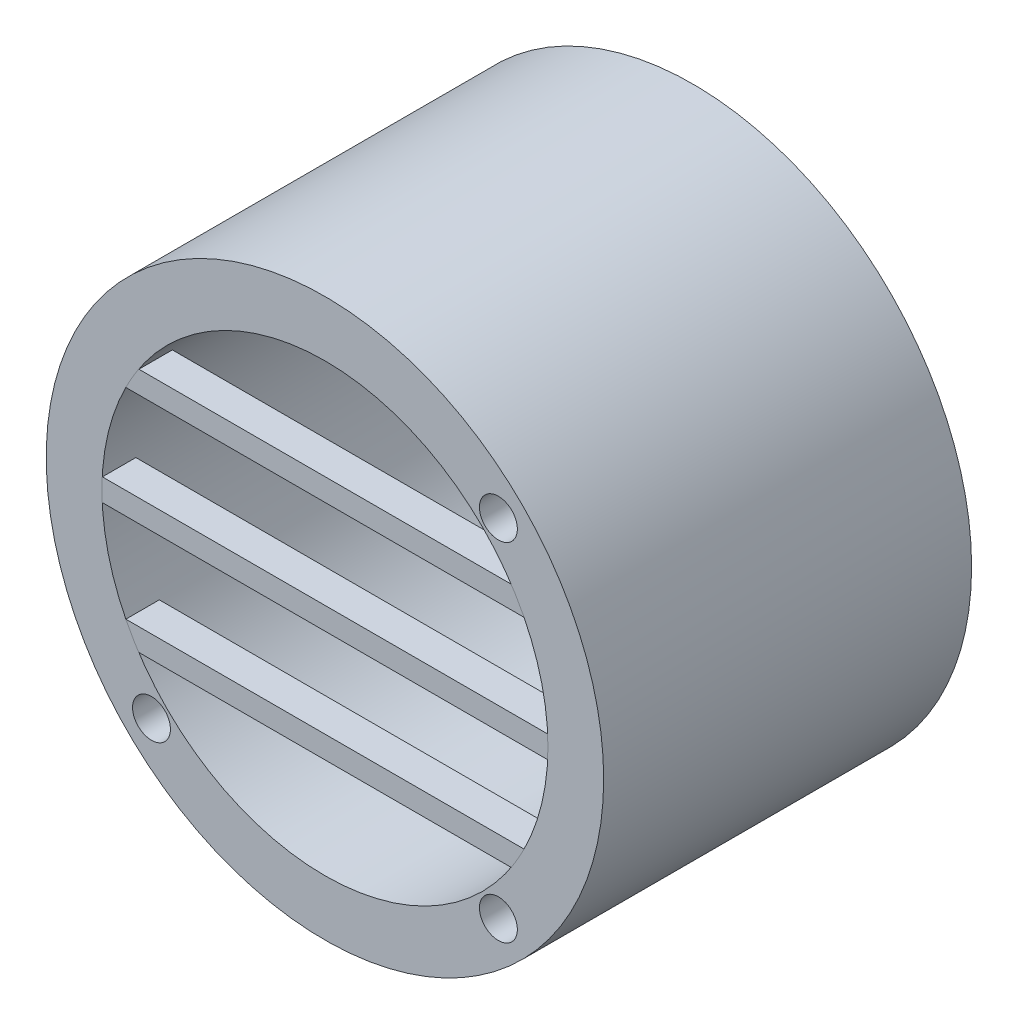
SolidWorks part; units mm, degrees
ref_plane "Front Plane" through (0, 0, 0) normal (0, 0, 1) x (1, 0, 0)
ref_plane "Top Plane" through (0, 0, 0) normal (0, 1, 0) x (1, 0, 0)
ref_plane "Right Plane" through (0, 0, 0) normal (1, 0, 0) x (0, 0, -1)
sketch "Sketch2" plane through (0, 0, 0) normal (0, 0, 1) x (1, 0, 0)
  circle A0 centre (0, 0) radius 25
  circle A1 centre (0, 0) radius 20
  dimension "D1" = 50
  dimension "D2" = 40
extrude "Boss-Extrude1" add sketch "Sketch2" along normal blind 33
sketch "Sketch3" plane through (0, 0, 33) normal (0, 0, 1) x (1, 0, 0)
  line L5 (-20, 0) -> (20, 0) construction
  line L6 (-20, -10) -> (20, -10)
  line L22 (-20, 10) -> (20, 10)
  line L24 (-20, -1) -> (20, -1)
  line L27 (-20, -1) -> (-20, 1)
  line L28 (-20, 1) -> (20, 1)
  line L29 (20, -1) -> (20, 1)
  line L30 (-20, -1) -> (20, 1) construction
  line L31 (-20, 1) -> (20, -1) construction
  line L32 (-20, 9) -> (20, 9)
  line L33 (-20, 9) -> (-20, 11)
  line L36 (-20, 11) -> (20, 11)
  line L37 (20, 9) -> (20, 11)
  line L38 (-20, 9) -> (20, 11) construction
  line L39 (-20, 11) -> (20, 9) construction
  line L42 (-20, -11) -> (20, -11)
  line L43 (-20, -11) -> (-20, -9)
  line L46 (-20, -9) -> (20, -9)
  line L47 (20, -11) -> (20, -9)
  line L50 (-20, -11) -> (20, -9) construction
  line L51 (-20, -9) -> (20, -11) construction
  circle A1 centre (0, 0) radius 20
  point P0 (0, 0)
  point P3 (0, 0)
  point P14 (0, 10)
  point P19 (0, -10)
  circle M11 centre (0, 0) radius 20
  dimension "D1" = 10
  dimension "D3" = 2
  dimension "D4" = 2
  dimension "D5" = 2
  dimension "D2" = 10
extrude "Boss-Extrude4" add sketch "Sketch3" against normal blind 3 separate body contours L32 L22 M11 | L36 L22 M11 | L28 L24 M11 | L46 L6 M11 | L42 L6 M11
hole_wizard "CBORE for M3 Hex Head Machine Screw1" positions "Sketch4" profile "Sketch5" counterbore size "M3" standard "ANSI Metric" end condition through all
sketch "Sketch4" plane through (11.2763, -30.4367, -10) normal (0, 0, -1) x (-1, 0, 0)
  point P3 (-4.2801, 45.993)
  point P6 (-4.2801, 14.8804)
  point P9 (26.8326, 14.8804)
  point P14 (0, 0)
sketch "Sketch5" plane through (15.5563, 15.5563, -10) normal (1, 0, 0) x (0, 1, 0)
  line L0 (0, 0) -> (0, 43)
  line L1 (0, 43) -> (1.7, 43)
  line L2 (1.7, 43) -> (1.7, 2.3)
  line L3 (4.2, 2.3) -> (1.7, 2.3)
  line L4 (4.2, 2.3) -> (4.2, 0.025)
  line L5 (4.2, 0.025) -> (4.225, 0)
  line L6 (4.225, 0) -> (0, 0)
  line L7 (-4.2, 0.025) -> (-4.225, 0) construction
  line L8 (0, -6.35) -> (0, 107.95) construction
  dimension "Thru Hole Dia." = 3.4
  dimension "Thru Hole Depth" = 43
  dimension "C'Bore Dia." = 8.4
  dimension "C'Bore Depth" = 2.3
  dimension "Near C'Sink Dia." = 8.45
  dimension "Near C'Sink Angle" = 90
